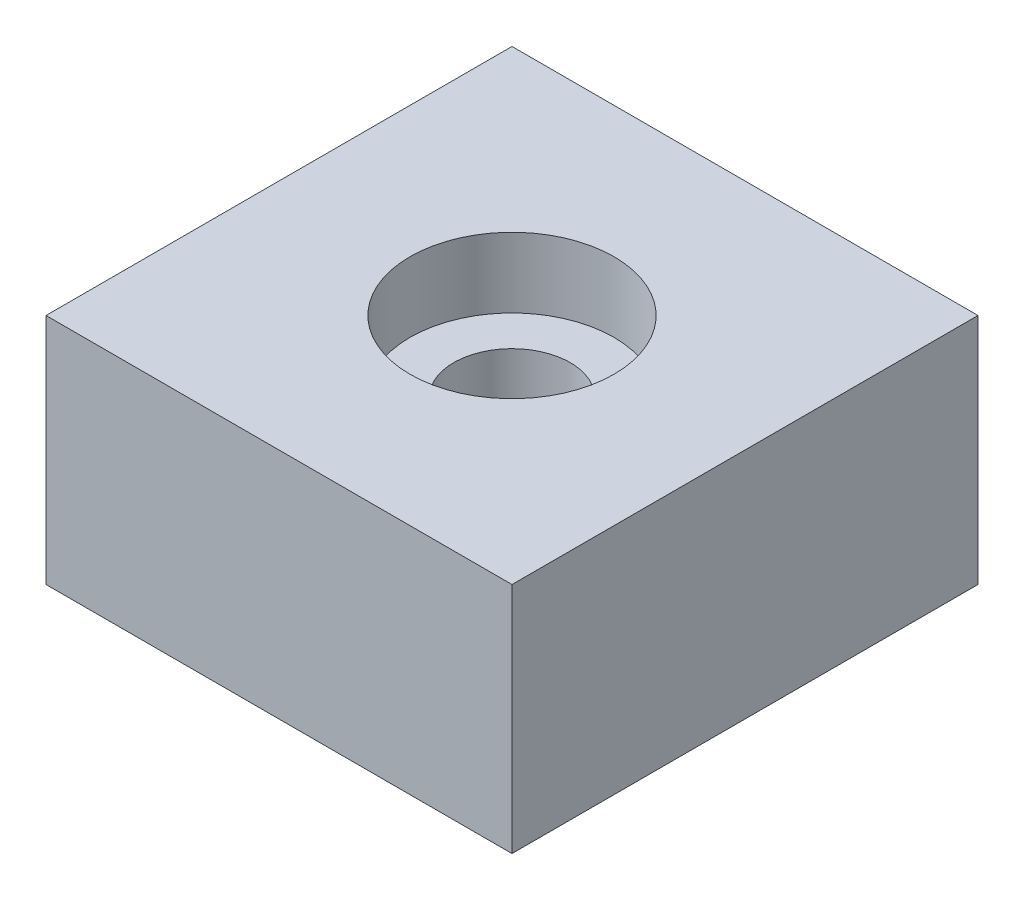
SolidWorks part; units mm, degrees
ref_plane "Front Plane" through (0, 0, 0) normal (0, 0, 1) x (1, 0, 0)
ref_plane "Top Plane" through (0, 0, 0) normal (0, 1, 0) x (1, 0, 0)
ref_plane "Right Plane" through (0, 0, 0) normal (1, 0, 0) x (0, 0, -1)
sketch "Sketch1" plane through (0, 0, 0) normal (0, 1, 0) x (1, 0, 0)
  line L1 (0, 0) -> (50.8, 0)
  line L2 (0, 0) -> (0, 50.8)
  line L3 (0, 50.8) -> (50.8, 50.8)
  line L4 (50.8, 0) -> (50.8, 50.8)
  dimension "D1" = 50.8
  dimension "D2" = 50.8
extrude "Boss-Extrude1" add sketch "Sketch1" along normal blind 25.4
sketch "Sketch6" plane through (0, 25.4, 0) normal (0, 1, 0) x (1, 0, 0)
  circle A0 centre (25.4, 25.4) radius 6.35
  dimension "D1" = 12.7
  dimension "D2" = 25.4
  dimension "D3" = 25.4
extrude "Cut-Extrude1" cut sketch "Sketch6" against normal blind 25.4
sketch "Sketch7" plane through (0, 25.4, 0) normal (0, 1, 0) x (1, 0, 0)
  circle A0 centre (25.4, 25.4) radius 11.1125
  dimension "D3" = 22.225
  dimension "D1" = 25.4
  dimension "D2" = 25.4
extrude "Cut-Extrude2" cut sketch "Sketch7" against normal blind 7.62
